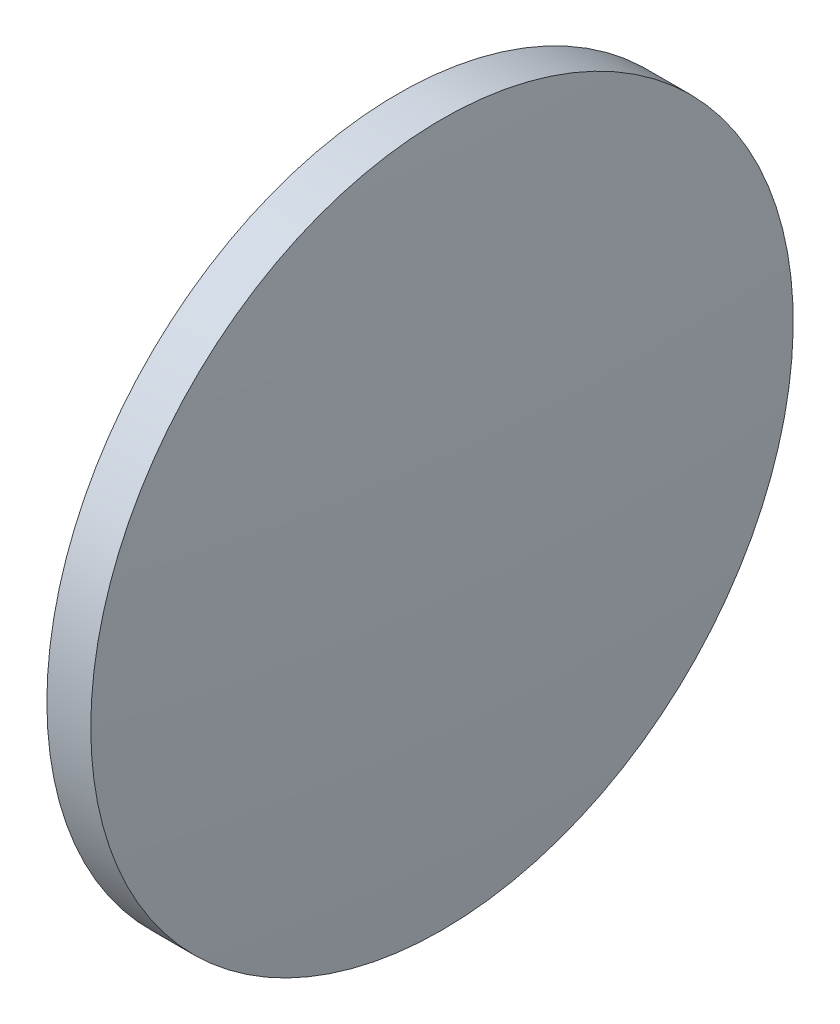
SolidWorks part; units mm, degrees
ref_plane "前视基准面" through (0, 0, 0) normal (0, 0, 1) x (1, 0, 0)
ref_plane "上视基准面" through (0, 0, 0) normal (0, 1, 0) x (1, 0, 0)
ref_plane "右视基准面" through (0, 0, 0) normal (1, 0, 0) x (0, 0, -1)
sketch "草图1" plane through (0, 0, 0) normal (0, 0, 1) x (1, 0, 0)
  line L0 (554.5689, 109.2775) -> (581.4604, 109.2775) construction
  line L1 (564.0754, 109.2775) -> (564.0754, 129.2775)
  line L2 (567.3554, 109.2775) -> (564.0754, 109.2775)
  line L5 (564.0754, 129.2775) -> (566.5754, 129.2775)
  arc A0 (567.3554, 109.2775) -> (566.5754, 129.2775) centre (310.5552, 109.2775) ccw
revolve "旋转1" add sketch "草图1" angle 360 about L0
